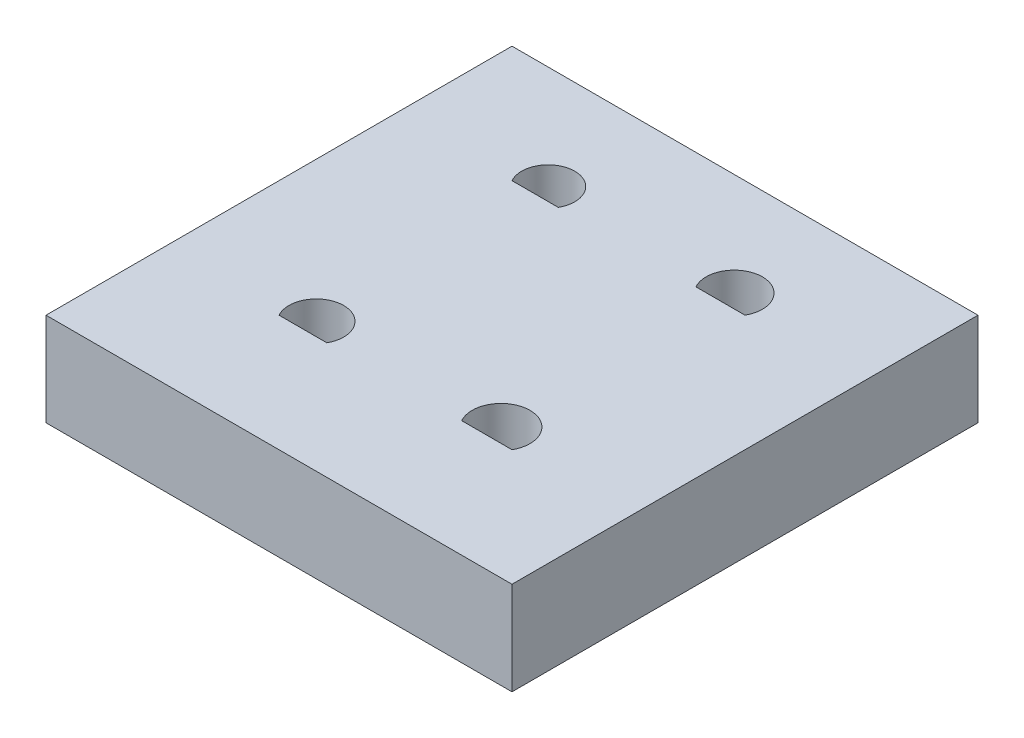
SolidWorks part; units mm, degrees
ref_plane "Front Plane" through (0, 0, 0) normal (0, 0, 1) x (1, 0, 0)
ref_plane "Top Plane" through (0, 0, 0) normal (0, 1, 0) x (1, 0, 0)
ref_plane "Right Plane" through (0, 0, 0) normal (1, 0, 0) x (0, 0, -1)
sketch "Sketch2" plane through (0, 0, 0) normal (0, 1, 0) x (1, 0, 0)
  line L1 (0, 0) -> (25.4, 0)
  line L2 (0, 0) -> (0, 25.4)
  line L3 (0, 25.4) -> (25.4, 25.4)
  line L4 (25.4, 0) -> (25.4, 25.4)
  line L5 (0, 0) -> (25.4, 25.4) construction
  line L6 (0, 25.4) -> (25.4, 0) construction
  point P4 (12.7, 12.7)
  dimension "D1" = 25.4
  dimension "D2" = 25.4
extrude "Boss-Extrude1" add sketch "Sketch2" along normal blind 5.08
sketch "Sketch3" plane through (0, 5.08, 5.08) normal (0, 1, 0) x (1, 0, 0)
  line L0 (6.35, 11.43) -> (8.9571, 11.43)
  line L4 (16.3079, 11.43) -> (19.05, 11.43)
  line L5 (6.35, 24.13) -> (8.8722, 24.13)
  line L6 (16.3754, 24.13) -> (19.05, 24.13)
  line L7 (0, 30.48) -> (0, 5.08) construction
  line L8 (25.4, 30.48) -> (0, 30.48) construction
  line L9 (25.4, 5.08) -> (25.4, 30.48) construction
  line L10 (0, 5.08) -> (25.4, 5.08) construction
  arc A0 (8.9571, 11.43) -> (6.35, 11.43) centre (7.6535, 12.159) ccw
  arc A4 (19.05, 11.43) -> (16.3079, 11.43) centre (17.6789, 12.2047) ccw
  arc A5 (8.8722, 24.13) -> (6.35, 24.13) centre (7.6111, 24.8412) ccw
  arc A6 (19.05, 24.13) -> (16.3754, 24.13) centre (17.7127, 24.8818) ccw
  dimension "D1" = 1.4935
  dimension "D3" = 1.5748
  dimension "D5" = 1.4478
  dimension "D7" = 1.5342
  dimension "D2" = 2.2225
  dimension "D4" = 2.3495
  dimension "D6" = 2.159
  dimension "D8" = 2.286
  dimension "D9" = 6.35
  dimension "D10" = 6.35
  dimension "D11" = 6.35
  dimension "D12" = 6.35
  dimension "D13" = 6.35
  dimension "D14" = 6.35
  dimension "D15" = 6.35
  dimension "D16" = 6.35
extrude "Cut-Extrude1" cut sketch "Sketch3" against normal blind 5.08
